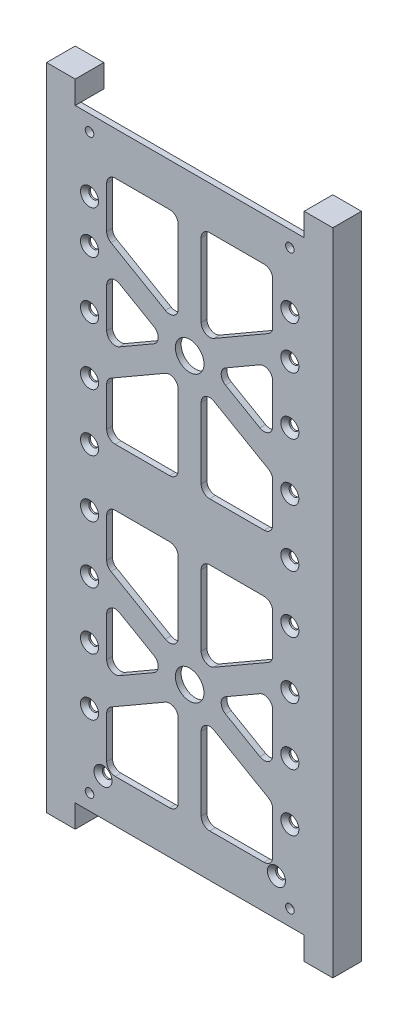
SolidWorks part; units mm, degrees
material "6061-T6 (SS)"
ref_plane "Front Plane" through (0, 0, 0) normal (0, 0, 1) x (1, 0, 0)
ref_plane "Top Plane" through (0, 0, 0) normal (0, 1, 0) x (1, 0, 0)
ref_plane "Right Plane" through (0, 0, 0) normal (1, 0, 0) x (0, 0, -1)
sketch "Sketch1" plane through (0, 0, 0) normal (0, 0, 1) x (1, 0, 0)
  line L1 (0, 0) -> (88, 0)
  line L2 (0, 0) -> (0, 211)
  line L3 (0, 211) -> (88, 211)
  line L4 (88, 0) -> (88, 211)
  dimension "D1" = 88
  dimension "D2" = 211
extrude "Boss-Extrude1" add sketch "Sketch1" along normal blind 2
sketch "Sketch2" plane through (0, 0, 2) normal (0, 0, 1) x (1, 0, 0)
  line L0 (0, 105.5) -> (88, 105.5) construction
  line L1 (0, 211) -> (0, 0) construction
  line L2 (88, 0) -> (88, 211) construction
  line L3 (44, 211) -> (44, 0) construction
  line L4 (88, 211) -> (0, 211) construction
  line L5 (0, 0) -> (88, 0) construction
  line L6 (0, 155.25) -> (88, 155.25) construction
  line L7 (0, 55.75) -> (88, 55.75) construction
  dimension "D1" = 55.75
  dimension "D2" = 55.75
sketch "Sketch3" plane through (0, 0, 2) normal (0, 0, 1) x (1, 0, 0)
  line L0 (0, 155.25) -> (88, 155.25) construction
  line L2 (0, 211) -> (0, 0) construction
  line L3 (15, 196) -> (73, 196)
  line L4 (15, 196) -> (15, 115.5)
  line L5 (15, 115.5) -> (73, 115.5)
  line L6 (73, 196) -> (73, 115.5)
  line L7 (88, 211) -> (0, 211) construction
  line L8 (88, 0) -> (88, 211) construction
  line L9 (0, 105.5) -> (88, 105.5) construction
  line L10 (40, 196) -> (40, 115.5)
  line L11 (48, 196) -> (48, 115.5)
  line L12 (44, 211) -> (44, 0) construction
  line L13 (73, 171.9932) -> (15, 138.5068) construction
  line L14 (15, 171.9932) -> (73, 138.5068) construction
  line L15 (73, 176.612) -> (15, 143.1256)
  line L16 (73, 167.3744) -> (15, 133.888)
  line L17 (15, 176.612) -> (73, 143.1256)
  line L18 (15, 167.3744) -> (73, 133.888)
  circle A0 centre (44, 155.25) radius 5
  dimension "D1" = 10
  dimension "D3" = 15
  dimension "D4" = 15
  dimension "D5" = 15
  dimension "D6" = 10
  dimension "D7" = 8
  dimension "D8" = 4
  dimension "D9" = 30
  dimension "D10" = 30
  dimension "D11" = 8
  dimension "D12" = 4
  dimension "D13" = 4
  dimension "D14" = 8
ref_plane "Plane1" through (0, 105.5, 0) normal (0, -1, 0) x (1, 0, 0)
extrude "Cut-Extrude2" cut sketch "Sketch3" against normal blind 2 contours L18 L11 L5 L6 | L10 L16 L4 L5 | L18 L4 L15 | L16 L17 L6 | L15 L6 L3 L11 | L4 L17 L10 L3
sketch "Sketch4" plane through (0, 0, 2) normal (0, 0, 1) x (1, 0, 0)
  line L0 (0, 155.25) -> (88, 155.25) construction
  circle A0 centre (44, 155.25) radius 5
  dimension "D1" = 10
extrude "Cut-Extrude3" cut sketch "Sketch4" against normal through all
mirror "Mirror2" about plane through (0, 105.5, 0) normal (0, -1, 0) of "Cut-Extrude3", "Cut-Extrude2"
fillet "Fillet2" radius 3 44 edges at (73, 67.8744, 1) (73, 43.6256, 1) (52, 55.75, 1) (40, 48.8218, 1) (40, 15, 1) (15, 15, 1) (15, 34.388, 1) (15, 143.1256, 1) (15, 167.3744, 1) (36, 155.25, 1) (15, 115.5, 1) (15, 133.888, 1) (40, 148.3218, 1) (40, 115.5, 1) (48, 196, 1) (73, 196, 1) (48, 162.1782, 1) (73, 115.5, 1) (48, 115.5, 1) (48, 148.3218, 1) (73, 133.888, 1) (15, 196, 1) (40, 196, 1) (40, 162.1782, 1) (15, 176.612, 1) (73, 167.3744, 1) (73, 143.1256, 1) (52, 155.25, 1) (48, 62.6782, 1) (48, 95.5, 1) (73, 95.5, 1) (73, 77.112, 1) (73, 34.388, 1) (73, 15, 1) (48, 15, 1) (48, 48.8218, 1) (40, 62.6782, 1) (15, 77.112, 1) (15, 95.5, 1) (40, 95.5, 1) (15, 43.6256, 1) (15, 67.8744, 1) (36, 55.75, 1) (73, 176.612, 1)
sketch "Sketch5" plane through (0, 0, 2) normal (0, 0, 1) x (1, 0, 0)
  line L0 (0, 205.5) -> (88, 205.5) construction
  line L1 (0, 211) -> (0, 0) construction
  line L2 (88, 0) -> (88, 211) construction
  line L3 (88, 211) -> (0, 211) construction
  line L4 (79, 211) -> (79, 0) construction
  line L5 (0, 0) -> (88, 0) construction
  line L6 (9, 211) -> (9, 0) construction
  line L7 (44, 211) -> (44, 0) construction
  line L8 (0, 5.5) -> (88, 5.5) construction
  line L9 (0, 105.5) -> (88, 105.5) construction
  circle A0 centre (9, 205.5) radius 1.5
  circle A1 centre (79, 205.5) radius 1.5
  circle A2 centre (9, 5.5) radius 1.5
  circle A3 centre (79, 5.5) radius 1.5
  dimension "D5" = 3
  dimension "D1" = 200
  dimension "D2" = 70
  dimension "D3" = 35
  dimension "D4" = 100
extrude "Cut-Extrude4" cut sketch "Sketch5" against normal through all
sketch "Sketch7" plane through (0, 0, 2) normal (0, 0, 1) x (1, 0, 0)
  line L0 (0, 105.5) -> (151.3859, 105.5) construction
  line L5 (0, 211) -> (0, 0) construction
  line L7 (44, 211) -> (44, 0) construction
  line L8 (88, 211) -> (0, 211) construction
  line L9 (0, 0) -> (88, 0) construction
  line L17 (94, 219) -> (84, 219)
  line L53 (88, 0) -> (88, 211)
  line L54 (84, 219) -> (84, 211)
  line L55 (84, 0) -> (88, 0)
  line L56 (94, 0) -> (94, 211)
  line L57 (94, -8) -> (94, 219)
  line L58 (88, 211) -> (0, 211) construction
  line L59 (84, 211) -> (88, 211)
  line L60 (84, -8) -> (84, 0)
  line L61 (94, -8) -> (84, -8)
  line L62 (-6, -8) -> (4, -8)
  line L63 (4, -8) -> (4, 0)
  line L64 (4, 0) -> (0, 0)
  line L65 (0, 0) -> (0, 211)
  line L66 (4, 211) -> (0, 211)
  line L67 (4, 219) -> (4, 211)
  line L68 (-6, 219) -> (4, 219)
  line L69 (-6, -8) -> (-6, 219)
  dimension "D1" = 6
extrude "Boss-Extrude2" add sketch "Sketch7" against normal blind 10
sketch "Sketch53" plane through (0, 0, -8) normal (0, 0, -1) x (-1, 0, 0)
  line L0 (-84, 0) -> (-84, 211)
  line L1 (-84, 211) -> (-90, 211)
  line L2 (-92, 209) -> (-92, 2)
  line L4 (-44, 0) -> (-44, 211)
  line L5 (-4, 0) -> (-84, 0) construction
  line L6 (-84, 211) -> (-4, 211) construction
  line L8 (-90, 0) -> (-84, 0)
  line L9 (4, 209) -> (4, 2)
  line L10 (-4, 211) -> (2, 211)
  line L11 (-4, 0) -> (-4, 211)
  line L12 (2, 0) -> (-4, 0)
  arc A0 (-92, 209) -> (-90, 211) centre (-90, 209) cw
  arc A1 (-90, 0) -> (-92, 2) centre (-90, 2) cw
  arc A2 (4, 209) -> (2, 211) centre (2, 209) ccw
  arc A3 (2, 0) -> (4, 2) centre (2, 2) ccw
  line M9 (-88, 0) -> (-88, 211)
  dimension "D1" = 2
  dimension "D2" = 2
extrude "Cut-Extrude5" cut sketch "Sketch53" against normal blind 8 contours A1 L8 L1 A0 L2 M9 | L12 A3 L9 A2 L10 L11
hole_wizard "CSK for M3 Flat Head Machine Screw1" positions "Sketch55" profile "Sketch56" countersink size "M3" standard "ANSI Metric"
sketch "Sketch55" plane through (0, 0, 2) normal (0, 0, 1) x (1, 0, 0)
  line L0 (-6, 219) -> (-6, -8) construction
  line L1 (84, 211) -> (4, 211) construction
  line L3 (44, 211) -> (44, 0) construction
  line L4 (4, 0) -> (84, 0) construction
  line L5 (4, 0) -> (84, 0) construction
  point P0 (9, 186)
  point P2 (9, 171)
  point P4 (9, 151)
  point P6 (9, 131)
  point P8 (9, 111)
  point P10 (9, 91)
  point P12 (9, 71)
  point P14 (9, 51)
  point P16 (9, 31)
  point P25 (13.7, 13)
  dimension "D2" = 25
  dimension "D3" = 40
  dimension "D4" = 60
  dimension "D5" = 80
  dimension "D6" = 100
  dimension "D7" = 120
  dimension "D8" = 140
  dimension "D9" = 160
  dimension "D10" = 180
  dimension "D12" = 19.7
  dimension "D13" = 13
  dimension "D14" = 35
sketch "Sketch56" plane through (9, 186, 2) normal (1, 0, 0) x (0, -1, 0)
  line L0 (0, 0) -> (0, 11.0215)
  line L1 (0, 11.0215) -> (1.7, 10)
  line L2 (1.7, 10) -> (1.7, 1.45)
  line L3 (1.7, 1.45) -> (3.15, 0)
  line L5 (3.15, 0) -> (0, 0)
  line L6 (-1.7, 1.45) -> (-3.15, 0) construction
  line L10 (0, 11.0215) -> (-1.7, 10) construction
  line L11 (0, -6.35) -> (0, 107.95) construction
  dimension "Hole Dia." = 3.4
  dimension "Hole Depth" = 10
  dimension "Near C'Sink Dia." = 6.3
  dimension "Near C'Sink Angle" = 90
  dimension "Drill Angle" = 118
ref_plane "Plane2" through (44, 0, 0) normal (-1, 0, 0) x (0, 0, 1)
mirror "Mirror3" about plane through (44, 0, 0) normal (-1, 0, 0) of "CSK for M3 Flat Head Machine Screw1"
ref_plane "Plane3" through (44, 0, 0) normal (1, 0, 0) x (0, 0, -1)
sketch "Sketch58" plane through (0, 0, 0) normal (0, 0, -1) x (-1, 0, 0)
  line L0 (-13.7, 13) -> (6, 13) construction
  line L1 (6, 219) -> (6, -8) construction
  circle A0 centre (-0.7, 13) radius 1.665
  dimension "D1" = 3.33
  dimension "D2" = 13
extrude "Cut-Extrude9" cut sketch "Sketch58" against normal blind 1.6 contours A0
mirror "Mirror4" about plane through (44, 0, 0) normal (1, 0, 0) of "Cut-Extrude9"
sketch "Sketch59" plane through (0, -8, 0) normal (0, -1, 0) x (-1, 0, 0)
  line L0 (1, 8) -> (1, -2) construction
  line L1 (6, 8) -> (-4, 8) construction
  line L2 (6, -2) -> (-4, -2) construction
  line L3 (6, 3) -> (-4, 3) construction
  line L6 (6, 8) -> (6, -2) construction
  line L7 (-4, 8) -> (-4, -2) construction
  circle A0 centre (1, 3) radius 2
  dimension "D2" = 4
  dimension "D1" = 5
extrude "Cut-Extrude10" cut sketch "Sketch59" against normal blind 10
ref_plane "Plane4" through (44, 0, 0) normal (-1, 0, 0) x (0, 0, 1)
mirror "Mirror5" about plane through (44, 0, 0) normal (-1, 0, 0) of "Cut-Extrude10"
